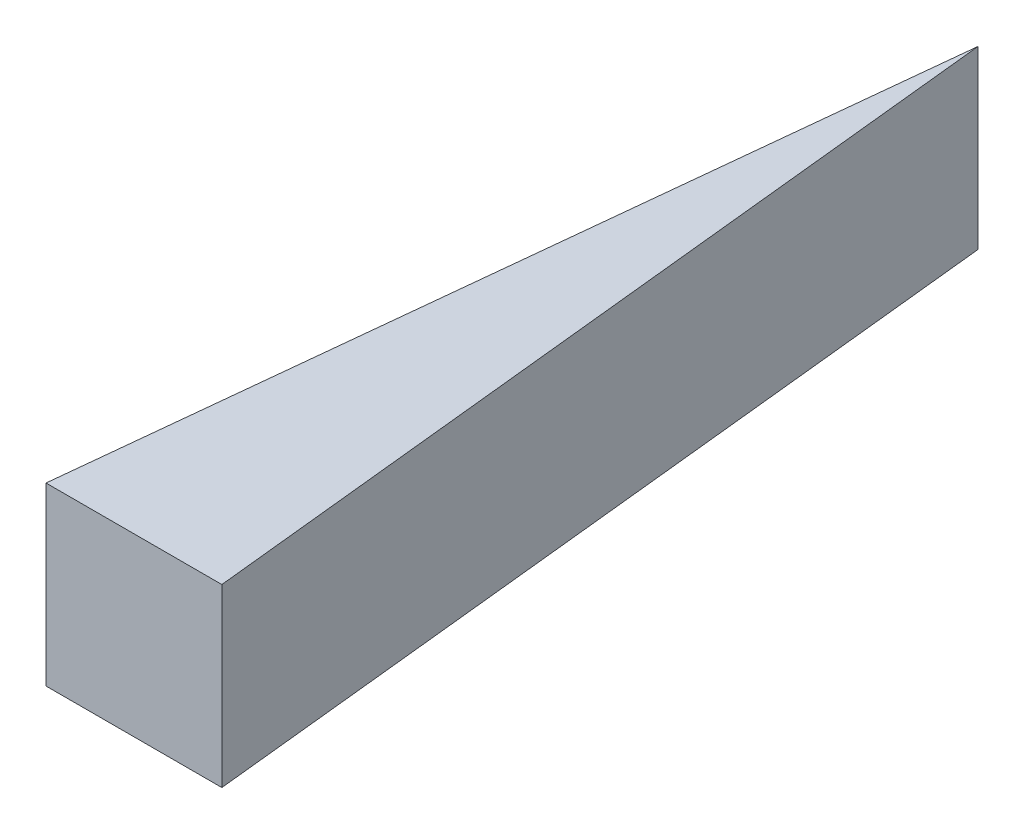
SolidWorks part; units mm, degrees
ref_plane "Front Plane" through (0, 0, 0) normal (0, 0, 1) x (1, 0, 0)
ref_plane "Top Plane" through (0, 0, 0) normal (0, 1, 0) x (1, 0, 0)
ref_plane "Right Plane" through (0, 0, 0) normal (1, 0, 0) x (0, 0, -1)
sketch "Sketch1" plane through (0, 0, 0) normal (0, 1, 0) x (1, 0, 0)
  line L0 (0, 24) -> (-2.5, 0)
  line L1 (-2.5, 0) -> (2.5, 0)
  line L2 (2.5, 0) -> (0, 24)
  dimension "D1" = 5
  dimension "D2" = 2.5
  dimension "D3" = 0
  dimension "D4" = 24
extrude "Boss-Extrude1" add sketch "Sketch1" along normal blind 5
